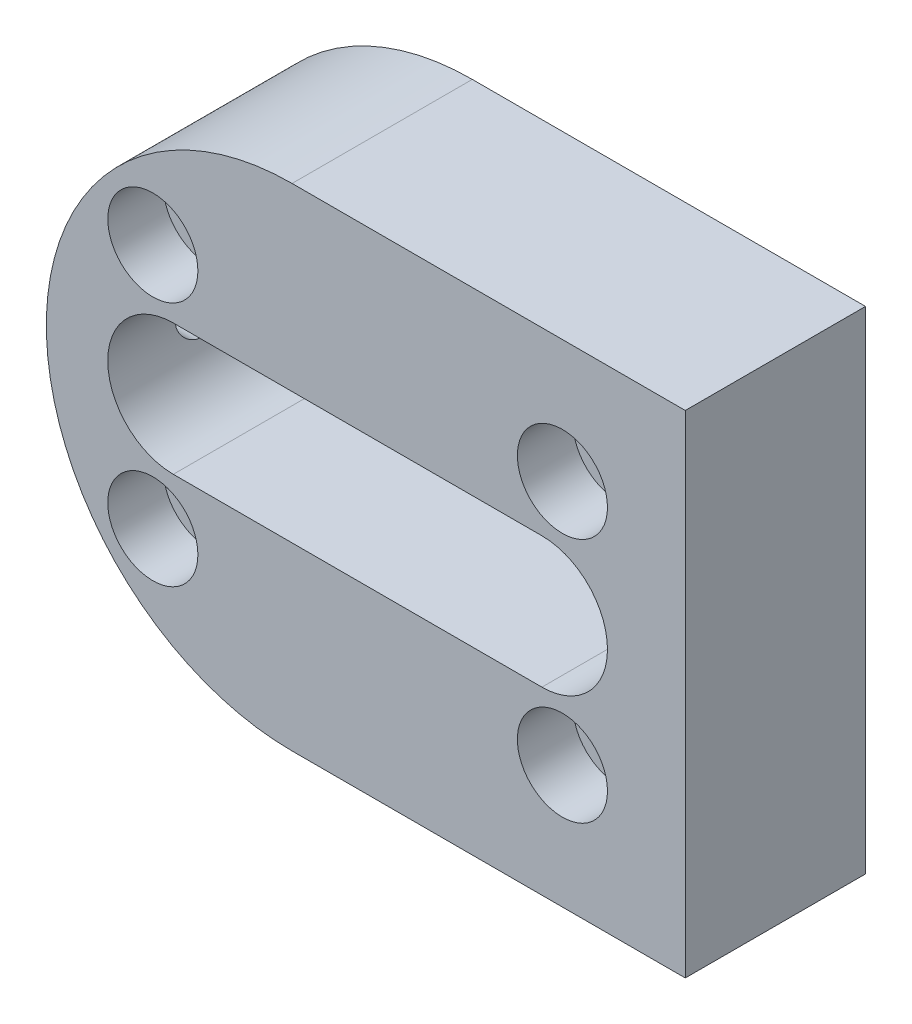
SolidWorks part; units mm, degrees
ref_plane "前视基准面" through (0, 0, 0) normal (0, 0, 1) x (1, 0, 0)
ref_plane "上视基准面" through (0, 0, 0) normal (0, 1, 0) x (1, 0, 0)
ref_plane "右视基准面" through (0, 0, 0) normal (1, 0, 0) x (0, 0, -1)
sketch "草图1" plane through (0, 0, 0) normal (0, 0, 1) x (1, 0, 0)
  line L0 (40, 0) -> (-120.2373, 0) construction
  line L1 (-8, 30) -> (40, 30)
  line L3 (-8, -30) -> (40, -30)
  line L4 (40, 30) -> (40, -30)
  line L5 (-22.5, 0) -> (22.5, 0) construction
  line L6 (-22.5, 8) -> (22.5, 8)
  line L7 (-22.5, -8) -> (22.5, -8)
  arc A1 (-8, 30) -> (-8, -30) centre (-8, 0) ccw
  arc A3 (-22.5, 8) -> (-22.5, -8) centre (-22.5, 0) ccw
  arc A4 (22.5, -8) -> (22.5, 8) centre (22.5, 0) ccw
  point P0 (0, 0)
  point P11 (0, 0)
  point P16 (0, 0)
  dimension "D2" = 40
  dimension "D4" = 30
  dimension "D5" = 45
  dimension "D1" = 60
  dimension "D3" = 48
  dimension "D6" = 16
extrude "凸台-拉伸1" add sketch "草图1" along normal blind 22
sketch "草图3" plane through (0, 0, 22) normal (0, 0, 1) x (1, 0, 0)
  line L1 (-25, 15) -> (25, 15)
  line L2 (-25, 15) -> (-25, -15)
  line L3 (-25, -15) -> (25, -15)
  line L4 (25, 15) -> (25, -15)
  line L5 (-25, 15) -> (25, -15) construction
  line L6 (-25, -15) -> (25, 15) construction
  point P0 (0, 0)
  dimension "D1" = 30
  dimension "D2" = 50
hole_wizard "打孔尺寸(%根据)内六角圆柱头螺钉的类型1" positions "3D草图1" profile "草图4" counterbore size "M6" standard "GB" end condition through all
sketch3d "3D草图1"
  point P0 (-25, 15, 22)
  point P3 (-25, -15, 22)
  point P6 (25, 15, 22)
  point P9 (25, -15, 22)
sketch "草图4" plane through (-25, 15, 22) normal (1, 0, 0) x (0, -1, 0)
  line L0 (0, 0) -> (0, 22)
  line L1 (0, 22) -> (3.3, 22)
  line L3 (3.3, 22) -> (3.3, 6.8)
  line L4 (3.3, 6.8) -> (5.5, 6.8)
  line L5 (5.5, 6.8) -> (5.5, 0)
  line L7 (5.5, 0) -> (0, 0)
  line L11 (0, -6.35) -> (0, 107.95) construction
  dimension "通孔孔直径" = 6.6
  dimension "通孔孔深度" = 22
  dimension "柱形沉头孔直径" = 11
  dimension "柱形沉头孔深度" = 6.8
sketch "草图5" plane through (0, 0, 0) normal (0, 0, -1) x (-1, 0, 0)
  circle A0 centre (0, 0) radius 23.5
  dimension "D1" = 47
ref_plane "基准面1" through (-38, 0, 0) normal (1, 0, 0) x (0, 0, -1)
hole_wizard "大小mm 暗销孔1" positions "3D草图3" profile "草图9" hole size "Ø1.0" standard "GB"
sketch3d "3D草图3"
  point P0 (-38, 0, 11)
  dimension "D1" = 11
  dimension "D2" = 8
sketch "草图9" plane through (-38, 0, 11) normal (0, 1, 0) x (0, 0, 1)
  line L0 (0, 0) -> (0, 7.5)
  line L1 (0, 7.5) -> (2.75, 7.5)
  line L2 (2.75, 7.5) -> (2.75, 0)
  line L5 (2.75, 0) -> (0, 0)
  line L11 (0, -6.35) -> (0, 107.95) construction
  dimension "通孔孔直径" = 5.5
  dimension "通孔孔深度" = 7.5
